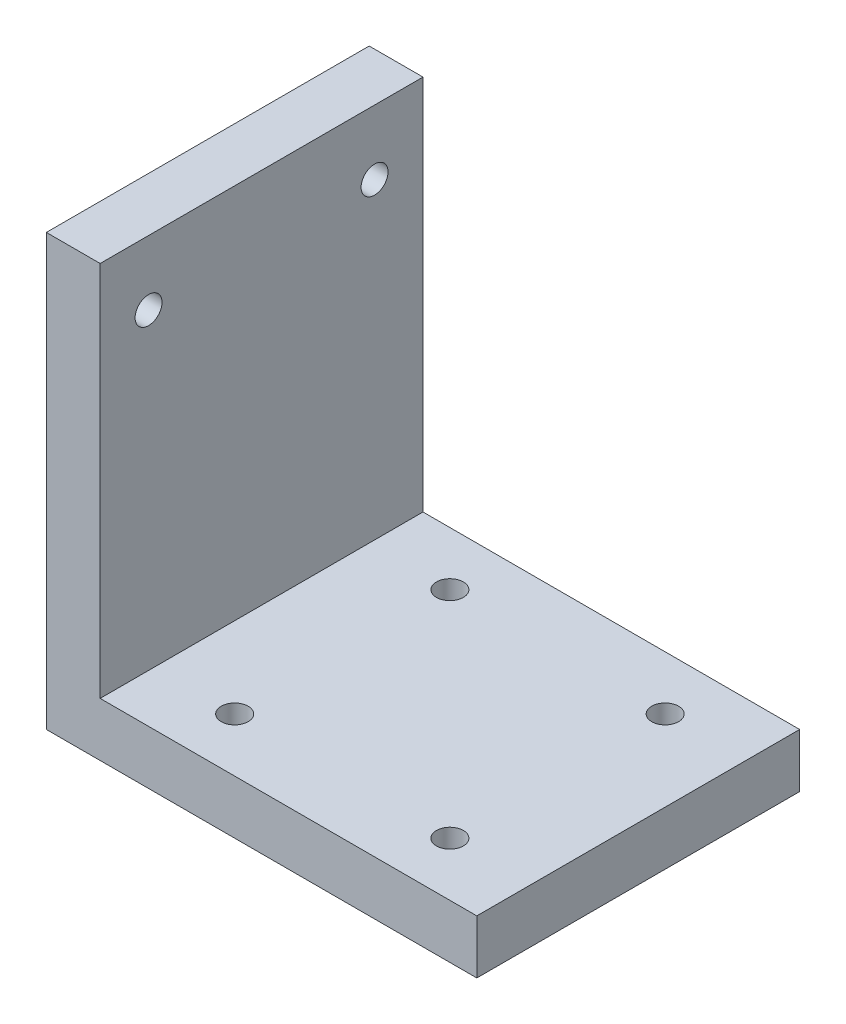
SolidWorks part; units mm, degrees
ref_plane "前视基准面" through (0, 0, 0) normal (0, 0, 1) x (1, 0, 0)
ref_plane "上视基准面" through (0, 0, 0) normal (0, 1, 0) x (1, 0, 0)
ref_plane "右视基准面" through (0, 0, 0) normal (1, 0, 0) x (0, 0, -1)
sketch "草图1" plane through (0, 0, 0) normal (0, 0, 1) x (1, 0, 0)
  line L0 (0, 80) -> (0, 0)
  line L1 (0, 0) -> (80, 0)
  line L2 (10, 80) -> (10, 10)
  line L3 (10, 10) -> (80, 10)
  line L4 (0, 80) -> (10, 80)
  line L5 (80, 10) -> (80, 0)
  dimension "D1" = 80
  dimension "D2" = 80
  dimension "D3" = 10
extrude "凸台-拉伸1" add sketch "草图1" along normal blind 60
sketch "草图2" plane through (0, 0, 0) normal (0, -1, 0) x (1, 0, 0)
  line L0 (80, 30) -> (3.0827, 30) construction
  line L1 (25, 50) -> (65, 50)
  line L2 (25, 50) -> (25, 10)
  line L3 (25, 10) -> (65, 10)
  line L4 (65, 50) -> (65, 10)
  line L5 (25, 50) -> (65, 10) construction
  line L6 (25, 10) -> (65, 50) construction
  line L7 (80, 60) -> (80, 0) construction
  point P0 (45, 30)
  point P9 (10.2736, 30)
  point P10 (0, 0)
  dimension "D1" = 40
  dimension "D2" = 40
  dimension "D3" = 15
hole_wizard "M6 螺纹孔1" positions "3D草图1" profile "草图3" tap size "M6" standard "GB"
sketch3d "3D草图1"
  point P0 (65, 0, 50)
  point P3 (65, 0, 10)
  point P6 (25, 0, 10)
  point P9 (25, 0, 50)
sketch "草图3" plane through (65, 0, 50) normal (1, 0, 0) x (0, 0, -1)
  line L0 (0, 0) -> (0, 16.5022)
  line L1 (0, 16.5022) -> (2.5, 15)
  line L2 (2.5, 15) -> (2.5, 0)
  line L5 (2.5, 0) -> (0, 0)
  line L10 (0, 16.5022) -> (-2.5, 15) construction
  line L11 (0, -6.35) -> (0, 107.95) construction
  dimension "螺纹孔钻头直径" = 5
  dimension "螺纹孔钻头深度" = 15
  dimension "导头角度" = 118
cosmetic thread "孔螺蚊线1"
cosmetic thread "孔螺蚊线2"
cosmetic thread "孔螺蚊线3"
cosmetic thread "孔螺蚊线4"
sketch "草图4" plane through (0, 0, 0) normal (-1, 0, 0) x (0, 0, 1)
  line L0 (30, 80) -> (30, 23.0207) construction
  line L1 (9, 68) -> (51, 68)
  line L2 (9, 68) -> (9, 28)
  line L3 (9, 28) -> (51, 28)
  line L4 (51, 68) -> (51, 28)
  line L5 (9, 68) -> (51, 28) construction
  line L6 (9, 28) -> (51, 68) construction
  line L7 (60, 80) -> (0, 80) construction
  point P0 (30, 48)
  point P10 (0, 0)
  point P11 (30, 46.8926)
  dimension "D1" = 42
  dimension "D2" = 40
  dimension "D3" = 12
hole_wizard "M6 螺纹孔2" positions "3D草图3" profile "草图5" tap size "M6" standard "GB"
sketch3d "3D草图3"
  point P0 (0, 68, 9)
  point P3 (0, 68, 51)
sketch "草图5" plane through (0, 68, 9) normal (0, 1, 0) x (0, 0, 1)
  line L0 (0, 0) -> (0, 16.5022)
  line L1 (0, 16.5022) -> (2.5, 15)
  line L2 (2.5, 15) -> (2.5, 0)
  line L5 (2.5, 0) -> (0, 0)
  line L10 (0, 16.5022) -> (-2.5, 15) construction
  line L11 (0, -6.35) -> (0, 107.95) construction
  dimension "螺纹孔钻头直径" = 5
  dimension "螺纹孔钻头深度" = 15
  dimension "导头角度" = 118
cosmetic thread "孔螺蚊线5"
cosmetic thread "孔螺蚊线6"
